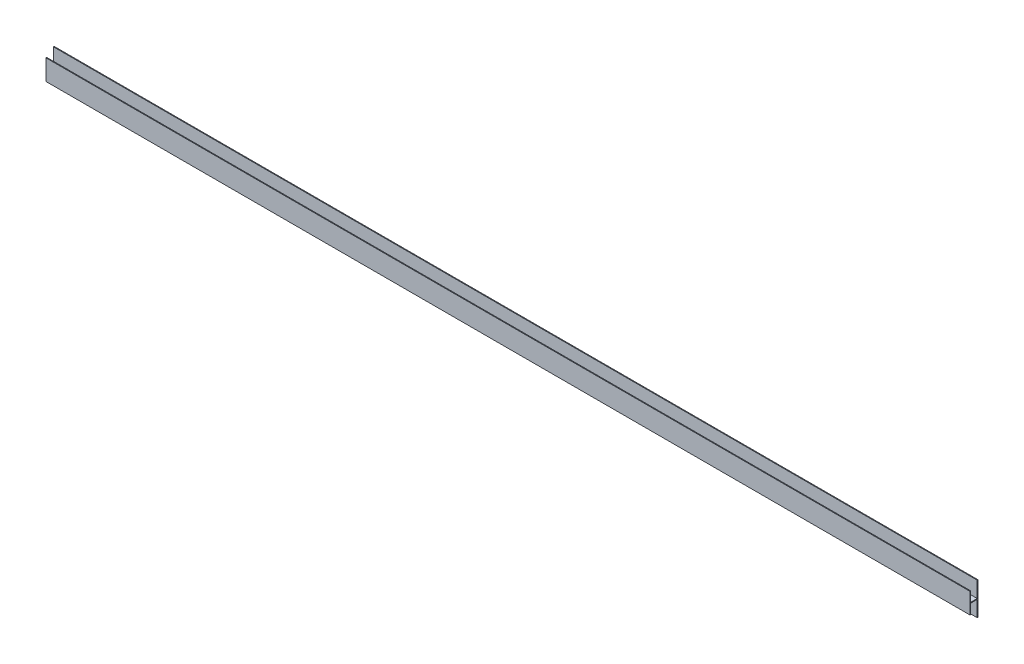
SolidWorks part; units mm, degrees
ref_plane "Front Plane" through (0, 0, 0) normal (0, 0, 1) x (1, 0, 0)
ref_plane "Top Plane" through (0, 0, 0) normal (0, 1, 0) x (1, 0, 0)
ref_plane "Right Plane" through (0, 0, 0) normal (1, 0, 0) x (0, 0, -1)
sketch "Sketch1" plane through (0, 0, 0) normal (1, 0, 0) x (0, 0, -1)
  line L0 (-7.1, 0) -> (7.1, 0) construction
  line L1 (7.1, -31.75) -> (7.1, 31.75) construction
  line L2 (-7.1, -20) -> (-7.1, 20) construction
  line L3 (-6.35, -0.75) -> (6.35, -0.75)
  line L4 (7.85, -31.75) -> (7.85, 31.75)
  line L5 (-6.35, -20) -> (-6.35, -0.75)
  line L6 (-6.35, 0.75) -> (6.35, 0.75)
  line L7 (6.35, -31.75) -> (6.35, -0.75)
  line L8 (-7.85, -20) -> (-7.85, 20)
  line L11 (7.85, -31.75) -> (6.35, -31.75)
  line L12 (7.85, 31.75) -> (6.35, 31.75)
  line L13 (-6.35, -20) -> (-7.85, -20)
  line L14 (-6.35, 20) -> (-7.85, 20)
  line L15 (-7.1, -0.75) -> (7.1, -0.75) construction
  line L16 (-7.1, 0.75) -> (7.1, 0.75) construction
  line L17 (-6.35, 0.75) -> (-6.35, 20)
  line L18 (-6.35, -20) -> (-6.35, 20) construction
  line L19 (6.35, 0.75) -> (6.35, 31.75)
  line L20 (6.35, -31.75) -> (6.35, 31.75) construction
  point P4 (0, 0)
  point P8 (7.1, 0)
  point P11 (-7.1, 0)
  dimension "D1" = 12.7
  dimension "D2" = 63.5
  dimension "D3" = 40
  dimension "D4" = 0.75
  dimension "D5" = 0.75
extrude "Boss-Extrude1" add sketch "Sketch1" along normal mid plane 1803.4
